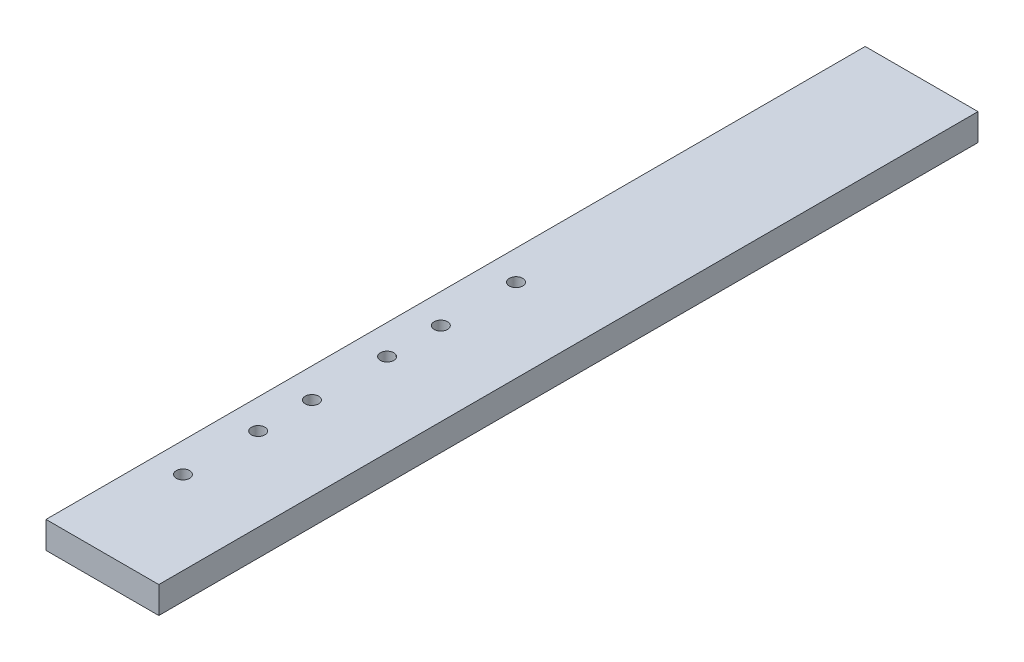
SolidWorks part; units mm, degrees
ref_plane "Front Plane" through (0, 0, 0) normal (0, 0, 1) x (1, 0, 0)
ref_plane "Top Plane" through (0, 0, 0) normal (0, 1, 0) x (1, 0, 0)
ref_plane "Right Plane" through (0, 0, 0) normal (1, 0, 0) x (0, 0, -1)
sketch "Sketch1" plane through (0, 0, 0) normal (0, 1, 0) x (1, 0, 0)
  line L1 (0, 0) -> (26.67, 0)
  line L2 (0, 0) -> (0, 193.675)
  line L3 (0, 193.675) -> (26.67, 193.675)
  line L4 (26.67, 0) -> (26.67, 193.675)
  dimension "D1" = 193.675
  dimension "D2" = 26.67
extrude "Boss-Extrude1" add sketch "Sketch1" along normal blind 6.35
sketch "Sketch3" plane through (0, 6.35, 0) normal (0, 1, 0) x (1, 0, 0)
  line L0 (0, 193.675) -> (0, 0) construction
  line L1 (0, 0) -> (26.67, 0) construction
  line L2 (0, 49.53) -> (26.67, 49.53) construction
  line L3 (26.67, 0) -> (26.67, 193.675) construction
  line L4 (0, 80.01) -> (26.67, 80.01) construction
  circle A0 centre (6.985, 25.4) radius 1.5875
  circle A1 centre (6.985, 43.18) radius 1.5875
  circle A2 centre (6.985, 73.66) radius 1.5875
  circle A3 centre (6.985, 55.88) radius 1.5875
  circle A4 centre (6.985, 104.14) radius 1.5875
  circle A5 centre (6.985, 86.36) radius 1.5875
  dimension "D2" = 3.175
  dimension "D4" = 3.175
  dimension "D1" = 6.985
  dimension "D3" = 25.4
  dimension "D5" = 17.78
  dimension "D6" = 6.35
  dimension "D7" = 6.35
extrude "Cut-Extrude1" cut sketch "Sketch3" against normal through all
